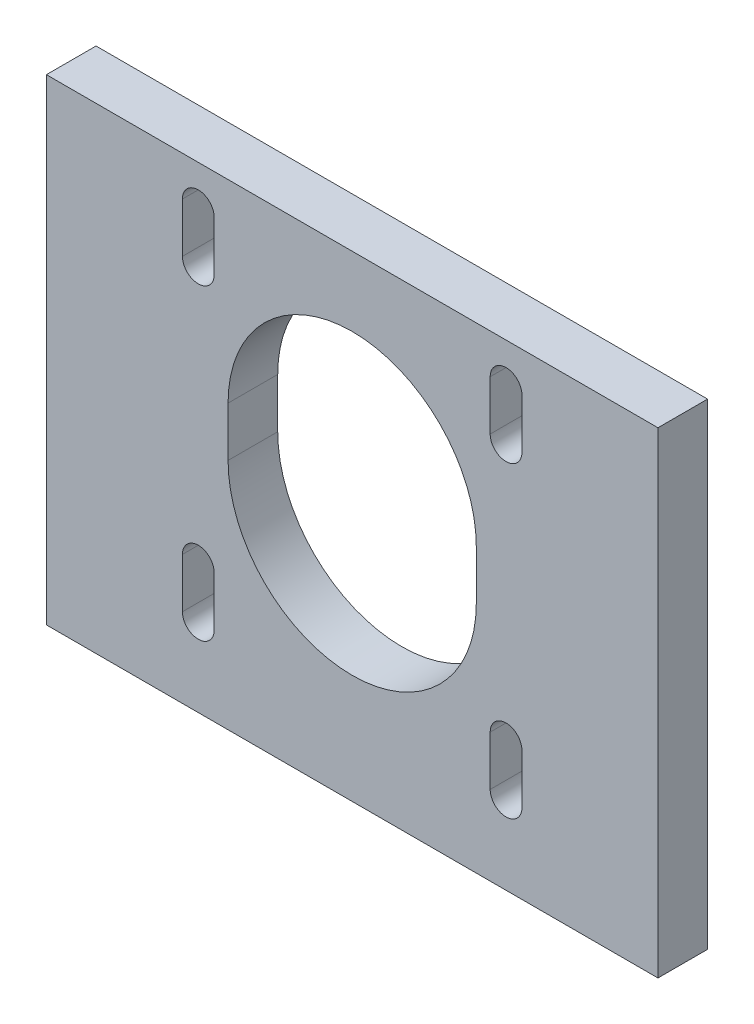
SolidWorks part; units mm, degrees
ref_plane "Front Plane" through (0, 0, 0) normal (0, 0, 1) x (1, 0, 0)
ref_plane "Top Plane" through (0, 0, 0) normal (0, 1, 0) x (1, 0, 0)
ref_plane "Right Plane" through (0, 0, 0) normal (1, 0, 0) x (0, 0, -1)
sketch "Sketch1" plane through (0, 0, 0) normal (0, 0, 1) x (1, 0, 0)
  line L0 (0, 0) -> (0, 60.7505) construction
  line L1 (30.8, 10) -> (-30.8, 10)
  line L2 (-30.8, 10) -> (-30.8, 52)
  line L3 (-30.8, 52) -> (30.8, 52)
  line L4 (30.8, 10) -> (30.8, 52)
  point P9 (0, 10)
  point P10 (0, 52)
  dimension "D1" = 10
  dimension "D2" = 30.8
  dimension "D3" = 42
extrude "Boss-Extrude1" add sketch "Sketch1" along normal blind 5
sketch "Sketch2" plane through (0, 0, 5) normal (0, 0, 1) x (1, 0, 0)
  line L0 (0, 52) -> (0, 10) construction
  line L1 (30.8, 52) -> (-30.8, 52) construction
  line L2 (-30.8, 10) -> (30.8, 10) construction
  line L3 (0, 30) -> (-30.8, 30) construction
  line L4 (-30.8, 52) -> (-30.8, 10) construction
  line L5 (12.5, 27.5) -> (-12.5, 27.5) construction
  line L6 (0, 30) -> (30.8, 30) construction
  line L7 (30.8, 10) -> (30.8, 52) construction
  line L8 (-12.5, 27.5) -> (-12.5, 32.5)
  line L9 (12.5, 27.5) -> (12.5, 32.5)
  line L10 (-15.5, 49.8263) -> (-15.5, 30.7643) construction
  line L11 (-13.9, 45.5) -> (-17.1, 45.5) construction
  line L12 (-17.1, 45.5) -> (-17.1, 48)
  line L13 (-17.1, 45.5) -> (-17.1, 43)
  line L14 (-13.9, 48) -> (-13.9, 45.5)
  line L15 (-13.9, 45.5) -> (-13.9, 43)
  line L16 (-17.1, 14.5) -> (-17.1, 12)
  line L17 (-17.1, 14.5) -> (-17.1, 17)
  line L18 (-13.9, 14.5) -> (-13.9, 17)
  line L19 (-13.9, 12) -> (-13.9, 14.5)
  line L20 (13.9, 12) -> (13.9, 14.5)
  line L21 (13.9, 14.5) -> (13.9, 17)
  line L22 (17.1, 14.5) -> (17.1, 17)
  line L23 (17.1, 14.5) -> (17.1, 12)
  line L24 (17.1, 45.5) -> (17.1, 48)
  line L25 (17.1, 45.5) -> (17.1, 43)
  line L26 (13.9, 45.5) -> (13.9, 43)
  line L27 (13.9, 48) -> (13.9, 45.5)
  arc A0 (-12.5, 27.5) -> (12.5, 27.5) centre (0, 27.5) ccw
  arc A1 (-12.5, 32.5) -> (12.5, 32.5) centre (0, 32.5) cw
  arc A2 (-17.1, 43) -> (-13.9, 43) centre (-15.5, 43) ccw
  arc A3 (-13.9, 48) -> (-17.1, 48) centre (-15.5, 48) ccw
  circle A4 centre (-15.5, 45.5) radius 1.6 construction
  arc A5 (-13.9, 12) -> (-17.1, 12) centre (-15.5, 12) cw
  arc A6 (-17.1, 17) -> (-13.9, 17) centre (-15.5, 17) cw
  arc A7 (17.1, 17) -> (13.9, 17) centre (15.5, 17) ccw
  arc A8 (13.9, 12) -> (17.1, 12) centre (15.5, 12) ccw
  arc A9 (13.9, 48) -> (17.1, 48) centre (15.5, 48) cw
  arc A10 (17.1, 43) -> (13.9, 43) centre (15.5, 43) cw
  point P17 (0, 27.5)
  point P19 (12.5, 30)
  point P22 (-12.5, 30)
  point P34 (-15.5, 45.5)
  dimension "D2" = 12.5
  dimension "D5" = 3.2
  dimension "D7" = 3.2
  dimension "D1" = 30
  dimension "D3" = 2.5
  dimension "D4" = 15.5
  dimension "D6" = 5
  dimension "D8" = 2.5
  dimension "D9" = 15.5
extrude "Cut-Extrude1" cut sketch "Sketch2" against normal blind 5
sketch "Sketch3" plane through (0, 0, 5) normal (0, 0, 1) x (1, 0, 0)
  line L0 (-30.8, 10) -> (30.8, 10)
  line L1 (30.8, 10) -> (30.8, 4)
  line L2 (30.8, 4) -> (-30.8, 4)
  line L3 (-30.8, 4) -> (-30.8, 10)
  dimension "D1" = 6
extrude "Boss-Extrude2" add sketch "Sketch3" against normal up to surface (5 mm away) up to face at (15.5, 45.5, 0)
